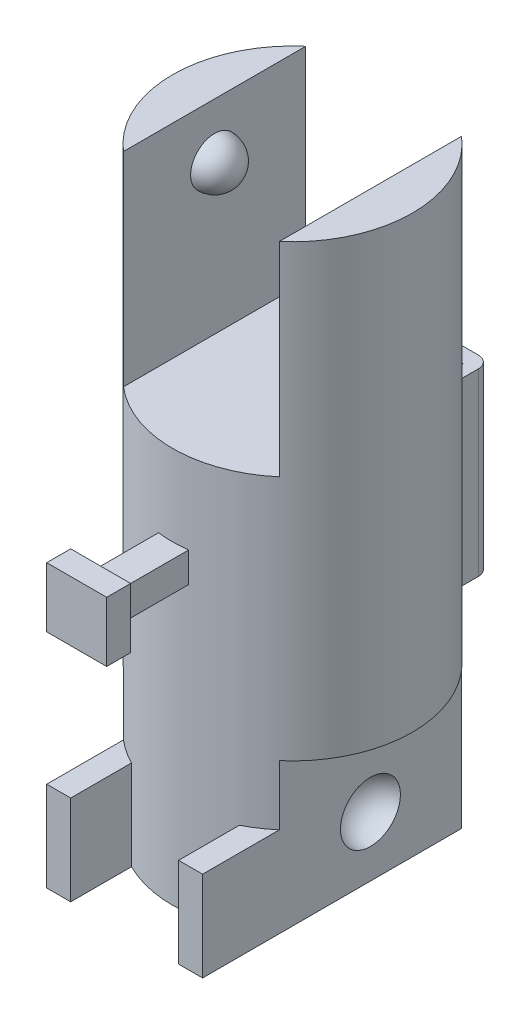
SolidWorks part; units mm, degrees
ref_plane "Front Plane" through (0, 0, 0) normal (0, 0, 1) x (1, 0, 0)
ref_plane "Top Plane" through (0, 0, 0) normal (0, 1, 0) x (1, 0, 0)
ref_plane "Right Plane" through (0, 0, 0) normal (1, 0, 0) x (0, 0, -1)
sketch "Sketch3" plane through (0, 0, 0) normal (0, 1, 0) x (1, 0, 0)
  circle A0 centre (0, 0) radius 10
  dimension "D1" = 20
extrude "Boss-Extrude3" add sketch "Sketch3" against normal blind 50 contours A0
sketch "Sketch6" plane through (0, 0, 0) normal (0, 1, 0) x (1, 0, 0)
  line L1 (-6.5, -10) -> (6.5, -10)
  line L2 (-6.5, -10) -> (-6.5, 10)
  line L3 (-6.5, 10) -> (6.5, 10)
  line L4 (6.5, -10) -> (6.5, 10)
  line L5 (-6.5, -10) -> (6.5, 10) construction
  line L6 (-6.5, 10) -> (6.5, -10) construction
  point P0 (0, 0)
  dimension "D1" = 20
  dimension "D2" = 13
extrude "Cut-Extrude4" cut sketch "Sketch6" against normal blind 17
ref_plane "Plane1" through (-6.5, 0, 0) normal (1, 0, 0) x (0, 0, -1)
sketch "Sketch7" plane through (-6.5, 0, 0) normal (1, 0, 0) x (0, 0, -1)
  line L0 (7.5993, 0) -> (-7.5993, 0) construction
  line L1 (7.5993, 0) -> (7.5993, -17) construction
  line L3 (0.0012, -2.5) -> (0.0012, -6.5)
  arc A1 (0.0012, -2.5) -> (0.0012, -6.5) centre (0.0012, -4.5) ccw
  dimension "D1" = 4.5
  dimension "D4" = 2
  dimension "D2" = 2.5
  dimension "D3" = 7.5982
  dimension "D5" = 4
revolve "Revolve4" add sketch "Sketch7" angle 360 about L3
ref_plane "Plane3" through (6.5, 0, 0) normal (-1, 0, 0) x (0, 0, 1)
ref_plane "Plane4" through (0, 0, 0) normal (-1, 0, 0) x (0, 0, 1)
mirror "Mirror1" about plane through (0, 0, 0) normal (-1, 0, 0) of "Revolve4"
sketch "Sketch10" plane through (0, -50, 0) normal (0, -1, 0) x (1, 0, 0)
  line L1 (-6.5, -10) -> (6.5, -10)
  line L2 (-6.5, -10) -> (-6.5, 10)
  line L3 (-6.5, 10) -> (6.5, 10)
  line L4 (6.5, -10) -> (6.5, 10)
  line L5 (-6.5, -10) -> (6.5, 10) construction
  line L6 (-6.5, 10) -> (6.5, -10) construction
  point P0 (0, 0)
extrude "Cut-Extrude5" cut sketch "Sketch10" against normal blind 12.5 flip side to cut
ref_plane "Plane5" through (-6.5, 0, 0) normal (-1, 0, 0) x (0, 0, 1)
sketch "Sketch13" plane through (-6.5, 0, 0) normal (-1, 0, 0) x (0, 0, 1)
  line L0 (-7.5993, -50) -> (7.5993, -50) construction
  line L1 (-7.5993, -50) -> (-7.5993, -37.5) construction
  line L2 (0, -42.5) -> (0, -47.5)
  arc A0 (0, -42.5) -> (0, -47.5) centre (0, -45) ccw
  dimension "D2" = 2.5
  dimension "D5" = 7.5993
  dimension "D1" = 5
  dimension "D3" = 7.5993
  dimension "D4" = 2.5
revolve "Cut-Revolve1" cut sketch "Sketch13" angle 360 about L2
ref_plane "Plane6" through (6.5, 0, 0) normal (1, 0, 0) x (0, 0, -1)
mirror "Mirror2" about plane through (0, 0, 0) normal (-1, 0, 0) of "Cut-Revolve1"
ref_plane "Plane7" through (0, 0, 10) normal (0, 0, 1) x (1, 0, 0)
sketch "Sketch14" plane through (0, 0, 10) normal (0, 0, 1) x (1, 0, 0)
  line L0 (-10, 0) -> (-10, -37.5) construction
  line L1 (-1.25, -26.25) -> (1.25, -26.25)
  line L2 (-1.25, -26.25) -> (-1.25, -23.75)
  line L3 (-1.25, -23.75) -> (1.25, -23.75)
  line L4 (1.25, -26.25) -> (1.25, -23.75)
  line L5 (-1.25, -26.25) -> (1.25, -23.75) construction
  line L6 (-1.25, -23.75) -> (1.25, -26.25) construction
  line L9 (-6.5, -50) -> (6.5, -50) construction
  point P0 (0, -25)
  dimension "D1" = 10
  dimension "D2" = 2.5
  dimension "D3" = 2.5
  dimension "D4" = 25
extrude "Boss-Extrude4" add sketch "Sketch14" along normal blind 6 and the other way up to surface contours L3 L4 L1 L2
ref_plane "Plane8" through (0, 0, 16) normal (0, 0, 1) x (1, 0, 0)
sketch "Sketch15" plane through (0, 0, 16) normal (0, 0, 1) x (1, 0, 0)
  line L0 (10, -37.5) -> (10, 0) construction
  line L1 (-2.5, -27.5) -> (2.5, -27.5)
  line L2 (-2.5, -27.5) -> (-2.5, -22.5)
  line L3 (-2.5, -22.5) -> (2.5, -22.5)
  line L4 (2.5, -27.5) -> (2.5, -22.5)
  line L5 (-2.5, -27.5) -> (2.5, -22.5) construction
  line L6 (-2.5, -22.5) -> (2.5, -27.5) construction
  line L7 (-6.5, -50) -> (6.5, -50) construction
  point P0 (0, -25)
  dimension "D1" = 10
  dimension "D2" = 5
  dimension "D3" = 5
  dimension "D4" = 25
extrude "Boss-Extrude5" add sketch "Sketch15" along normal blind 2
ref_plane "Plane9" through (0, 0, -10) normal (0, 0, -1) x (-1, 0, 0)
sketch "Sketch16" plane through (0, 0, -10) normal (0, 0, -1) x (-1, 0, 0)
  line L0 (10, -37.5) -> (10, 0) construction
  line L1 (-2.5, -36.5) -> (2.5, -36.5)
  line L2 (-2.5, -36.5) -> (-2.5, -21.5)
  line L3 (-2.5, -21.5) -> (2.5, -21.5)
  line L4 (2.5, -36.5) -> (2.5, -21.5)
  line L5 (-2.5, -36.5) -> (2.5, -21.5) construction
  line L6 (-2.5, -21.5) -> (2.5, -36.5) construction
  line L7 (6.5, -17) -> (-6.5, -17) construction
  point P0 (0, -29)
  dimension "D1" = 15
  dimension "D2" = 10
  dimension "D3" = 5
  dimension "D4" = 12
extrude "Boss-Extrude6" add sketch "Sketch16" along normal blind 4 and the other way up to surface contours L2 L3 L4 L1
fillet "Fillet2" radius 1 1 edges at (2.5, -29, -14)
fillet "Fillet3" radius 1 1 edges at (-2.5, -29, -14)
sketch "Sketch17" plane through (0, -21.5, 0) normal (0, 1, 0) x (1, 0, 0)
  line L0 (2.5, 13) -> (2.5, 9.6825) construction
  line L1 (-1.5, 10.25) -> (1.5, 10.25)
  line L2 (-1.5, 10.25) -> (-1.5, 12.75)
  line L3 (-1.5, 12.75) -> (1.5, 12.75)
  line L4 (1.5, 10.25) -> (1.5, 12.75)
  line L5 (-1.5, 10.25) -> (1.5, 12.75) construction
  line L6 (-1.5, 12.75) -> (1.5, 10.25) construction
  line L7 (1.5, 14) -> (-1.5, 14) construction
  point P0 (0, 11.5)
  dimension "D1" = 2.5
  dimension "D2" = 3
  dimension "D3" = 2.5
  dimension "D4" = 2.5
extrude "Cut-Extrude6" cut sketch "Sketch17" against normal through all
sketch "Sketch18" plane through (-6.5, 0, 0) normal (-1, 0, 0) x (0, 0, 1)
  line L0 (7.5993, -50) -> (13.9993, -50)
  line L1 (13.9993, -50) -> (13.9993, -42.5)
  line L2 (13.9993, -42.5) -> (7.5993, -42.5)
  line L3 (7.5993, -37.5) -> (7.5993, -50) construction
  line L4 (7.5993, -42.5) -> (7.5993, -50)
  dimension "D1" = 6.4
  dimension "D2" = 7.5
extrude "Boss-Extrude7" add sketch "Sketch18" against normal blind 2
mirror "Mirror3" about plane through (0, 0, 0) normal (1, 0, 0) of "Boss-Extrude7"
